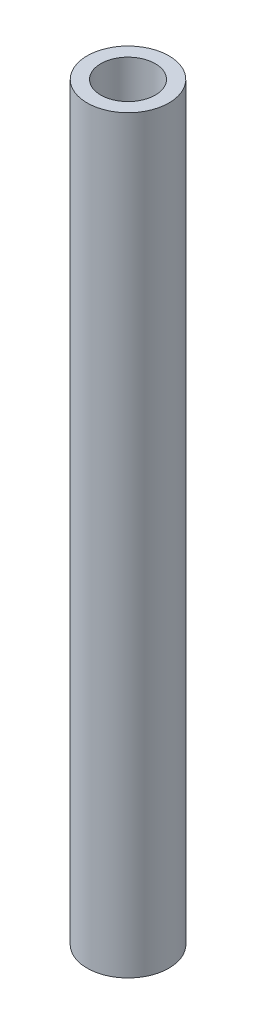
SolidWorks part; units mm, degrees
material "acero"
ref_plane "Alzado" through (0, 0, 0) normal (0, 0, 1) x (1, 0, 0)
ref_plane "Planta" through (0, 0, 0) normal (0, 1, 0) x (1, 0, 0)
ref_plane "Vista lateral" through (0, 0, 0) normal (1, 0, 0) x (0, 0, -1)
sketch "Croquis1" plane through (0, 0, 0) normal (0, 0, 1) x (1, 0, 0)
  line L0 (0, -0.7202) -> (0, 0.7202)
  line L2 (3, -27.5) -> (-3, -27.5)
  line L3 (3, -27.5) -> (3, 27.5)
  line L4 (3, 27.5) -> (-3, 27.5)
  line L5 (-3, -27.5) -> (-3, 27.5)
  line L6 (3, -27.5) -> (-3, 27.5) construction
  line L7 (3, 27.5) -> (-3, -27.5) construction
  line L8 (2, -27.5) -> (-2, -27.5)
  line L9 (2, -27.5) -> (2, 27.5)
  line L10 (2, 27.5) -> (-2, 27.5)
  line L11 (-2, -27.5) -> (-2, 27.5)
  line L12 (2, -27.5) -> (-2, 27.5) construction
  line L13 (2, 27.5) -> (-2, -27.5) construction
  line L15 (2.6, 25.5582) -> (3.25, 25.5582)
  line L16 (-3.25, 27.5) -> (-2.6, 27.5)
  point P1 (0, 0)
  point P3 (0, 0)
  dimension "D1" = 6
  dimension "D2" = 4
  dimension "D3" = 55
revolve "Revolución1" add sketch "Croquis1" angle 360 about L0
